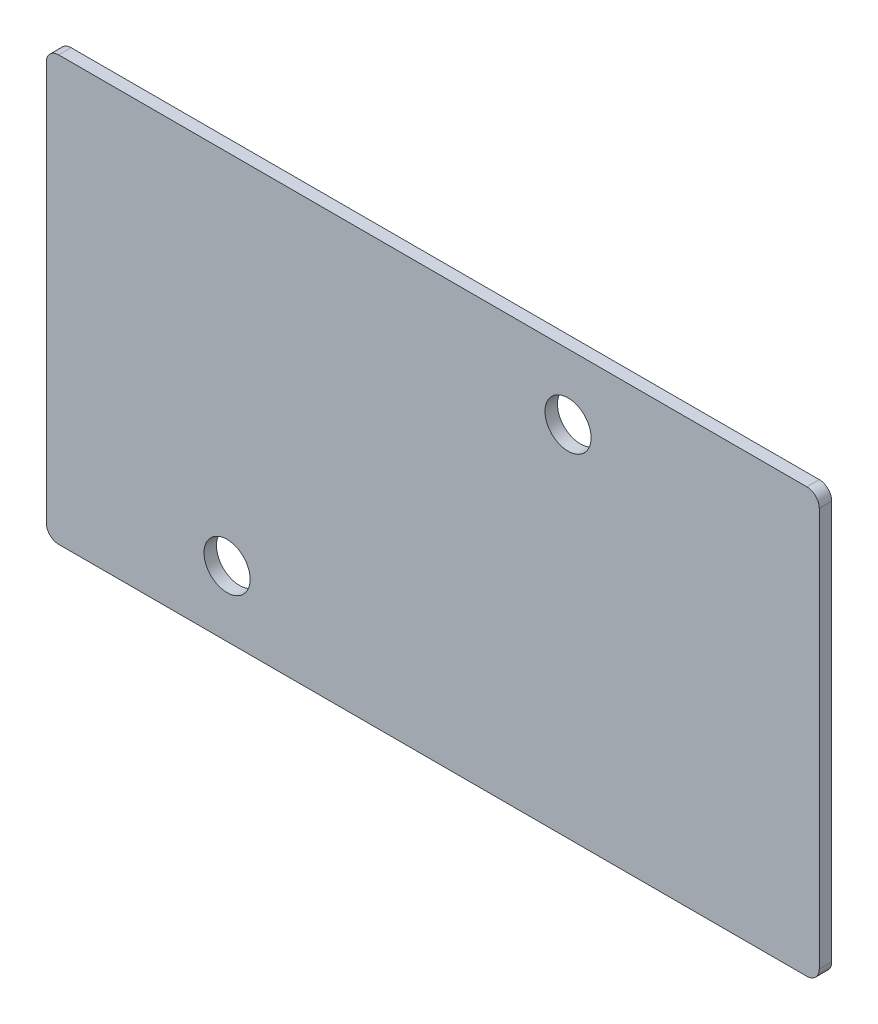
SolidWorks part; units mm, degrees
ref_plane "Alzado" through (0, 0, 0) normal (0, 0, 1) x (1, 0, 0)
ref_plane "Planta" through (0, 0, 0) normal (0, 1, 0) x (1, 0, 0)
ref_plane "Vista lateral" through (0, 0, 0) normal (1, 0, 0) x (0, 0, -1)
sketch "Croquis1" plane through (0, 0, 0) normal (0, 0, 1) x (1, 0, 0)
  line L0 (-5, 31.75) -> (55, 31.75)
  line L1 (0, 0) -> (40, 0) construction
  line L2 (0, 0) -> (0, 29.5) construction
  line L3 (0, 29.5) -> (40, 29.5) construction
  line L4 (40, 0) -> (40, 29.5) construction
  line L5 (56, -1.25) -> (56, 30.75)
  line L6 (-5, -2.25) -> (55, -2.25)
  line L7 (-6, -1.25) -> (-6, 30.75)
  circle A0 centre (35.85, 26.5) radius 1.85
  circle A1 centre (8.5, 3) radius 1.85
  arc A2 (-6, -1.25) -> (-5, -2.25) centre (-5, -1.25) ccw
  arc A3 (55, -2.25) -> (56, -1.25) centre (55, -1.25) ccw
  arc A4 (56, 30.75) -> (55, 31.75) centre (55, 30.75) ccw
  arc A5 (-5, 31.75) -> (-6, 30.75) centre (-5, 30.75) ccw
  dimension "D3" = 3.7
  dimension "D4" = 3
  dimension "D5" = 4.15
  dimension "D6" = 8.5
  dimension "D7" = 3
  dimension "D9" = 1
  dimension "D1" = 40
  dimension "D2" = 29.5
  dimension "D8" = 2.25
  dimension "D10" = 6
  dimension "D11" = 2.25
  dimension "D12" = 16
  dimension "D13" = 62
  dimension "D14" = 34
extrude "Saliente-Extruir1" add sketch "Croquis1" along normal blind 1
sketch "Croquis2" plane through (0, 0, 1) normal (0, 0, 1) x (1, 0, 0)
  line L0 (0, 29.5) -> (40, 29.5) construction
  line L1 (0, 0) -> (0, 29.5) construction
  circle A0 centre (10.5, 25.5) radius 2.75
  dimension "D1" = 5.5
  dimension "D2" = 4
  dimension "D3" = 10.5
extrude "Cortar-Extruir1" [suppressed] cut sketch "Croquis2" against normal through all
